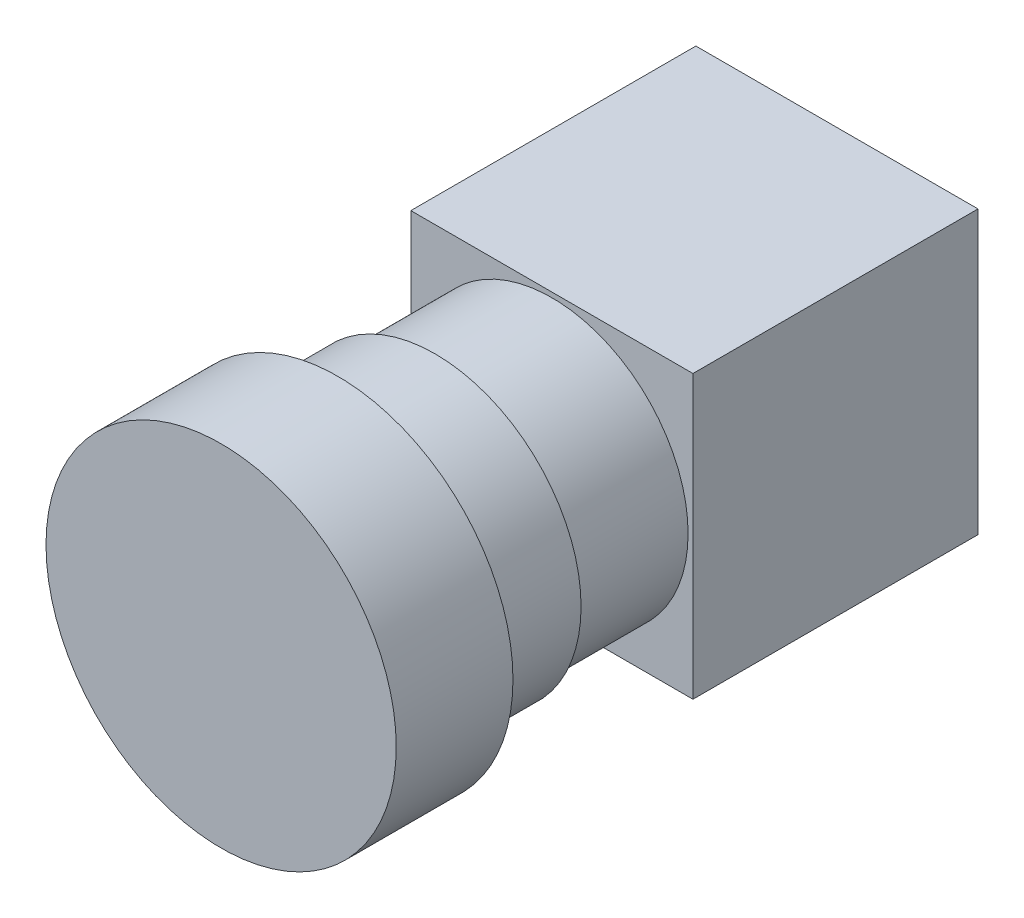
SolidWorks part; units mm, degrees
ref_plane "前视基准面" through (0, 0, 0) normal (0, 0, 1) x (1, 0, 0)
ref_plane "上视基准面" through (0, 0, 0) normal (0, 1, 0) x (1, 0, 0)
ref_plane "右视基准面" through (0, 0, 0) normal (1, 0, 0) x (0, 0, -1)
sketch "草图3" plane through (0, 0, 0) normal (0, 0, 1) x (1, 0, 0)
  line L1 (-14.5, 14.5) -> (14.5, 14.5)
  line L2 (-14.5, 14.5) -> (-14.5, -14.5)
  line L3 (-14.5, -14.5) -> (14.5, -14.5)
  line L4 (14.5, 14.5) -> (14.5, -14.5)
  line L5 (-14.5, 14.5) -> (14.5, -14.5) construction
  line L6 (-14.5, -14.5) -> (14.5, 14.5) construction
  point P0 (0, 0)
  dimension "D1" = 29
  dimension "D2" = 29
extrude "凸台-拉伸2" add sketch "草图3" along normal blind 29.3
sketch "草图4" plane through (0, 0, 29.3) normal (0, 0, 1) x (1, 0, 0)
  circle A0 centre (0, 0) radius 14
  dimension "D1" = 28
extrude "凸台-拉伸3" add sketch "草图4" along normal blind 12
sketch "草图5" plane through (0, 0, 41.3) normal (0, 0, 1) x (1, 0, 0)
  circle A0 centre (0, 0) radius 15
  dimension "D1" = 30
extrude "凸台-拉伸4" add sketch "草图5" along normal blind 10
sketch "草图6" plane through (0, 0, 51.3) normal (0, 0, 1) x (1, 0, 0)
  circle A0 centre (0, 0) radius 18
  dimension "D1" = 36
extrude "凸台-拉伸5" add sketch "草图6" along normal blind 12
sketch "草图7" plane through (0, -14.5, 0) normal (0, -1, 0) x (1, 0, 0)
  line L0 (0, 0) -> (0, 29.3) construction
  line L5 (-14.5, 0) -> (14.5, 0) construction
  line L6 (-14.5, 29.3) -> (14.5, 29.3) construction
  line L7 (-9.85, 26.15) -> (9.85, 26.15)
  line L8 (-9.85, 26.15) -> (-9.85, 3.15)
  line L9 (-9.85, 3.15) -> (9.85, 3.15)
  line L10 (9.85, 26.15) -> (9.85, 3.15)
  line L11 (-9.85, 26.15) -> (9.85, 3.15) construction
  line L12 (-9.85, 3.15) -> (9.85, 26.15) construction
  circle A0 centre (9.85, 26.15) radius 1.5
  circle A3 centre (-9.85, 26.15) radius 1.5
  circle A4 centre (0, 3.15) radius 1.5
  point P4 (0, 14.65)
  dimension "D3" = 3
  dimension "D4" = 3
  dimension "D5" = 3
  dimension "D1" = 23
  dimension "D2" = 19.7
extrude "切除-拉伸1" cut sketch "草图7" against normal blind 5 contours L7 A3 L8 | L8 A3 L7 | L7 A0 L10 | L10 A0 L7 | L9 A4 | L9 A4
